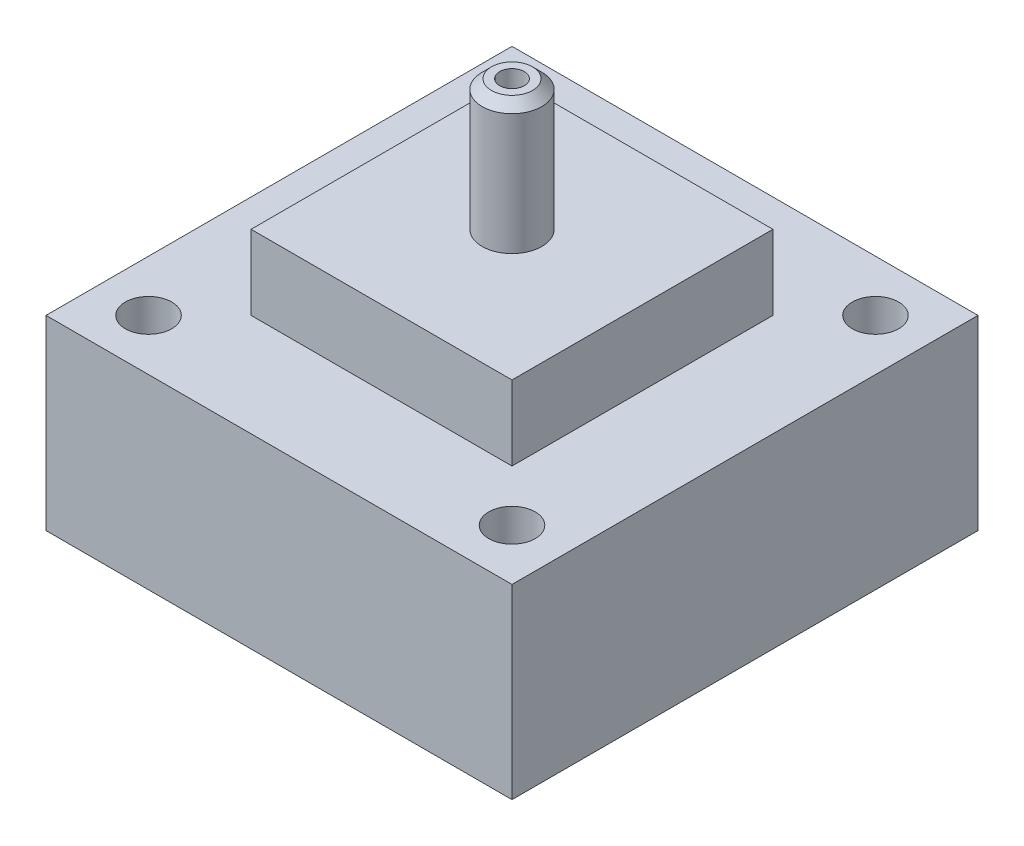
SolidWorks part; units mm, degrees
other "Markup2"
sketch "Sketch7" plane through (-12.5, 11, 12.5) normal (-0.3501, 0.7717, 0.531) x (0.0642, -0.5457, 0.8355)
other "DetailItem2"
ref_plane "Front Plane" through (0, 0, 0) normal (0, 0, 1) x (1, 0, 0)
ref_plane "Top Plane" through (0, 0, 0) normal (0, 1, 0) x (1, 0, 0)
ref_plane "Right Plane" through (0, 0, 0) normal (1, 0, 0) x (0, 0, -1)
sketch "Sketch1" plane through (0, 0, 0) normal (0, 1, 0) x (1, 0, 0)
  line L0 (-7, -7) -> (7, -7)
  line L1 (-7, -7) -> (-7, 7)
  line L2 (7, -7) -> (7, 7)
  line L3 (-7, 7) -> (7, 7)
  line L4 (-7, -7) -> (7, 7) construction
  line L5 (7, -7) -> (-7, 7) construction
  point P1 (0, 0)
  dimension "D1" = 14
extrude "Boss-Extrude1" add sketch "Sketch1" along normal blind 4
sketch "Sketch2" plane through (0, 0, 0) normal (0, -1, 0) x (1, 0, 0)
  line L0 (-12.5, -12.5) -> (-12.5, 12.5)
  line L1 (-12.5, -12.5) -> (12.5, -12.5)
  line L2 (-12.5, 12.5) -> (12.5, 12.5)
  line L3 (12.5, -12.5) -> (12.5, 12.5)
  line L4 (-12.5, -12.5) -> (12.5, 12.5) construction
  line L5 (-12.5, 12.5) -> (12.5, -12.5) construction
  line L6 (-0.1744, 7) -> (-0.1744, 12.5) construction
  line L7 (-7, 7) -> (7, 7) construction
  circle A0 centre (-9.75, 9.75) radius 1.2446
  circle A1 centre (9.75, 9.75) radius 1.2446
  circle A2 centre (9.75, -9.75) radius 1.2446
  circle A3 centre (-9.75, -9.75) radius 1.2446
  point P1 (0, 0)
  point P13 (-0.1744, 9.75)
  point P17 (0, 0)
  point P20 (0, 0)
  point P23 (0, 0)
  point P25 (0, 0)
  dimension "D2" = 2.4892
  dimension "D1" = 25
  dimension "D3" = 4
extrude "Boss-Extrude2" add sketch "Sketch2" along normal blind 10
sketch "Sketch3" plane through (0, -10, 0) normal (0, -1, 0) x (1, 0, 0)
  line L0 (-12.5, 12.5) -> (12.5, -12.5) construction
  circle A0 centre (0, 0) radius 4.23
  dimension "D1" = 8.46
extrude "Cut-Extrude1" cut sketch "Sketch3" against normal blind 9.8
sketch "Sketch4" plane through (0, 0, 0) normal (1, 0, 0) x (0, 0, -1)
  line L0 (0, 4) -> (0, 6.6565) construction
  line L1 (-7, 4) -> (7, 4) construction
  line L2 (0.6604, 11) -> (0.6604, 4)
  line L3 (0.6604, 4) -> (1.6, 4)
  line L4 (1.6, 4) -> (1.6, 10.5)
  line L5 (1.6, 10.5) -> (1.1, 11)
  line L6 (1.1, 11) -> (0.6604, 11)
  dimension "D1" = 7
  dimension "D2" = 1.6
  dimension "D3" = 45
  dimension "D4" = 0.5
  dimension "D5" = 0.6604
revolve "Revolve1" add sketch "Sketch4" angle 360 about L0
sketch "Sketch5" plane through (0, 4, 0) normal (0, 1, 0) x (1, 0, 0)
  circle A0 centre (0, 0) radius 0.6604
extrude "Cut-Extrude2" cut sketch "Sketch5" against normal up to surface (14 mm away) up to face at (0, -10, -4.23)
